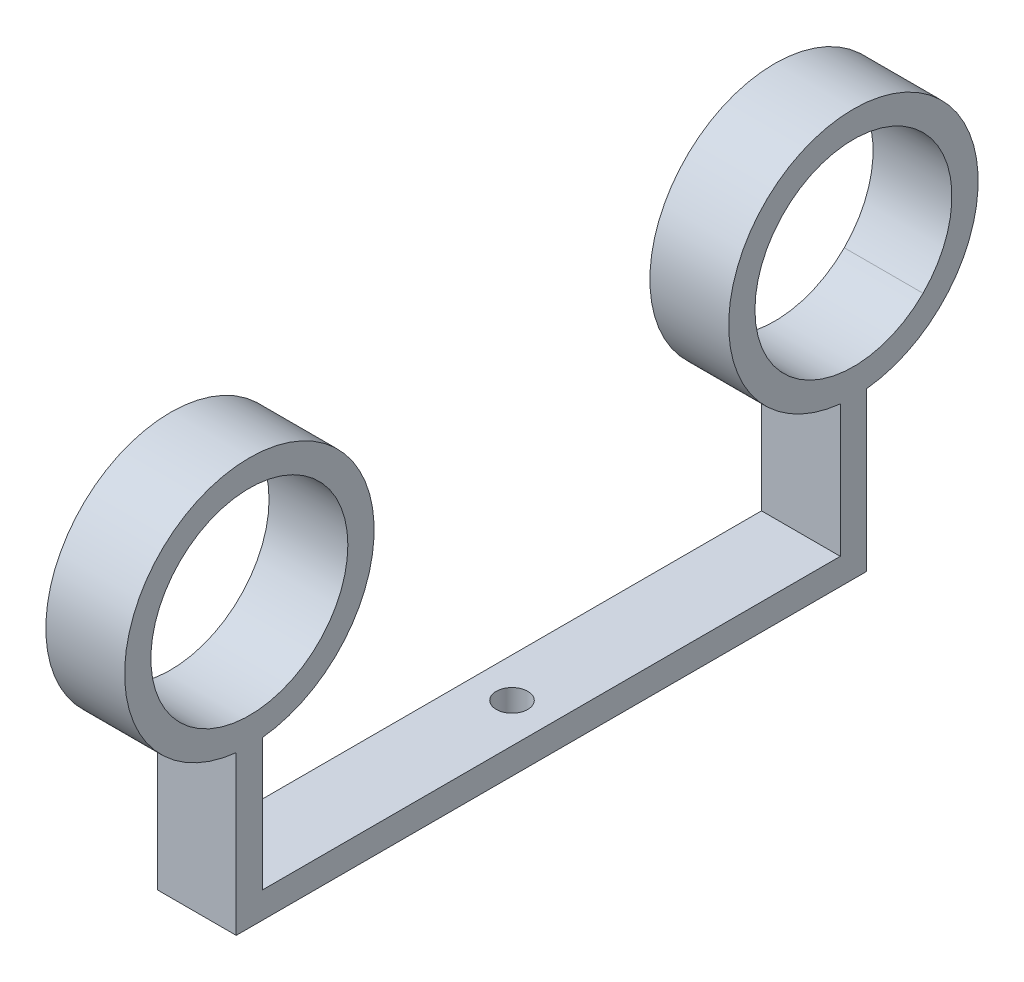
SolidWorks part; units mm, degrees
material "Cast Alloy Steel"
ref_plane "Front Plane" through (0, 0, 0) normal (0, 0, 1) x (1, 0, 0)
ref_plane "Top Plane" through (0, 0, 0) normal (0, 1, 0) x (1, 0, 0)
ref_plane "Right Plane" through (0, 0, 0) normal (1, 0, 0) x (0, 0, -1)
sketch "Sketch1" plane through (0, 0, 0) normal (1, 0, 0) x (0, 0, -1)
  line L0 (0, 150) -> (0, 0) construction
  line L1 (0, 0) -> (120, 0)
  line L2 (120, 0) -> (120, 70)
  dimension "D1" = 120
  dimension "D2" = 70
  dimension "D3" = 150
extrude "Extrude-Thin2" add sketch "Sketch1" along normal blind 30 thin thin type one direction reverse wall 10
sketch "Sketch2" plane through (30, 0, 0) normal (1, 0, 0) x (0, 0, -1)
  line L0 (110, 70) -> (120, 70) construction
  line L1 (115, 107.5) -> (115, 70) construction
  circle A0 centre (115, 107.5) radius 37.5
  point P7 (115, 70)
  dimension "D1" = 75
extrude "Extrude-Thin3" add sketch "Sketch2" against normal up to surface (30 mm away) thin
mirror "Mirror1" about plane through (30, 0, 0) normal (0, 0, 1) of bodies 104
sketch "Sketch3" plane through (0, 10, 0) normal (0, 1, 0) x (1, 0, 0)
  line L0 (0, 0) -> (30, 0) construction
  line L1 (30, -110) -> (30, 110) construction
  circle A0 centre (15, 0) radius 6
  dimension "D1" = 12
extrude "Cut-Extrude1" cut sketch "Sketch3" against normal through all and the other way through all
sketch "Sketch6" plane through (30, 0, 0) normal (1, 0, 0) x (0, 0, -1)
  text T0 "If you are reading this, you are awesome! Do suppress the sentence out, though. "
extrude "Writing on the wall" [suppressed] cut sketch "Sketch6" against normal blind 1
sketch "Sketch7" plane through (0, 0, 0) normal (0, 0, 1) x (1, 0, 0)
  line L0 (15, 110) -> (15, 0) construction
  line L1 (30, 0) -> (0, 0) construction
  circle A0 centre (15, 110) radius 5
  dimension "D1" = 10
  dimension "D2" = 110
extrude "Support Rod" [suppressed] add sketch "Sketch7" along normal up to next and the other way up to next
sketch "Sketch8" plane through (0, 0, 0) normal (1, 0, 0) x (0, 0, -1)
  line L0 (115, 155) -> (115, -15.4412) construction
  line L1 (67.5, 107.5) -> (162.5, 107.5) construction
  line L2 (115, 107.5) -> (148.5876, 141.0876)
  line L3 (115, 107.5) -> (148.5876, 73.9124)
  line L4 (0, 16.5) -> (0, -16.5) construction
  line L5 (-115, 107.5) -> (-148.5876, 73.9124)
  line L6 (-115, 107.5) -> (-148.5876, 141.0876)
  arc A0 (120, 60.2639) -> (110, 60.2639) centre (115, 107.5) ccw construction
  dimension "D1" = 90
  dimension "D2" = 45
split line "Split Line1"
